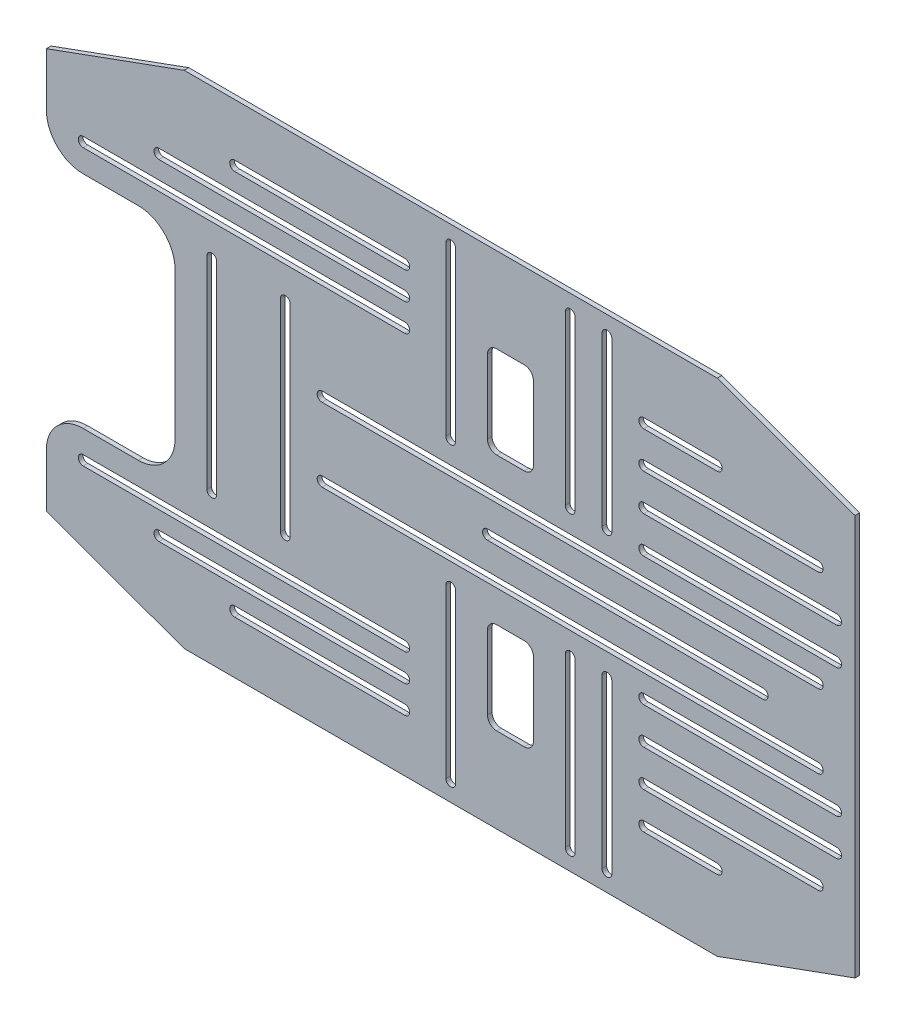
SolidWorks part; units mm, degrees
material "6061-T6 (SS)"
ref_plane "Front Plane" through (0, 0, 0) normal (0, 0, 1) x (1, 0, 0)
ref_plane "Top Plane" through (0, 0, 0) normal (0, 1, 0) x (1, 0, 0)
ref_plane "Right Plane" through (0, 0, 0) normal (1, 0, 0) x (0, 0, -1)
sketch "Sketch1" plane through (0, 0, 0) normal (0, 0, 1) x (1, 0, 0)
  line L0 (-279.4, 138.3894) -> (-184.2141, 173.0342)
  line L2 (-184.2141, 173.0342) -> (184.2141, 173.0342)
  line L3 (-254, 147.6342) -> (254, 147.6342) construction
  line L4 (184.2141, 173.0342) -> (279.4, 138.3894)
  line L5 (279.4, 138.3894) -> (279.4, -138.3894)
  line L10 (-254, 147.6342) -> (-254, -147.6342) construction
  line L11 (279.4, -138.3894) -> (184.2141, -173.0342)
  line L12 (184.2141, -173.0342) -> (-184.2141, -173.0342)
  line L13 (-254, -147.6342) -> (254, -147.6342) construction
  line L14 (-184.2141, -173.0342) -> (-279.4, -138.3894)
  line L16 (-279.4, -76.2) -> (-190.5, -76.2)
  line L17 (-190.5, -76.2) -> (-190.5, 76.2)
  line L18 (-190.5, 76.2) -> (-279.4, 76.2)
  line L19 (-279.4, 76.2) -> (-279.4, 138.3894)
  line L20 (254, 147.6342) -> (254, -147.6342) construction
  line L24 (-279.4, -138.3894) -> (-279.4, -76.2)
  point P6 (0, 147.6342)
  point P7 (-254, 0)
  point P13 (-190.5, 0)
  dimension "D1" = 508
  dimension "D2" = 295.2684
  dimension "D3" = 20
  dimension "D4" = 20
  dimension "D5" = 20
  dimension "D6" = 20
  dimension "D7" = 25.4
  dimension "D8" = 25.4
  dimension "D9" = 25.4
  dimension "D10" = 152.4
  dimension "D11" = 88.9
extrude "Boss-Extrude1" add sketch "Sketch1" along normal blind 3.175
fillet "Fillet3" radius 25.4 4 edges at (-279.4, 76.2, 1.5875) (-190.5, 76.2, 1.5875) (-190.5, -76.2, 1.5875) (-279.4, -76.2, 1.5875)
sketch "Sketch4" plane through (0, 0, 3.175) normal (0, 0, 1) x (1, 0, 0)
  line L0 (-254, 95.25) -> (-31.75, 95.25) construction
  line L1 (-254, 98.6282) -> (-31.75, 98.6282)
  line L2 (-254, 91.8718) -> (-31.75, 91.8718)
  line L3 (-201.6606, 114.3) -> (-31.75, 114.3) construction
  line L4 (-201.6606, 117.6782) -> (-31.75, 117.6782)
  line L5 (-201.6606, 110.9218) -> (-31.75, 110.9218)
  line L6 (-149.3211, 133.35) -> (-31.75, 133.35) construction
  line L7 (-149.3211, 136.7282) -> (-31.75, 136.7282)
  line L8 (-149.3211, 129.9718) -> (-31.75, 129.9718)
  line L9 (-165.1, 69.85) -> (-165.1, -69.85) construction
  line L10 (-161.7218, 69.85) -> (-161.7218, -69.85)
  line L11 (-168.4782, 69.85) -> (-168.4782, -69.85)
  line L12 (-114.3, 69.85) -> (-114.3, -69.85) construction
  line L13 (-110.9218, 69.85) -> (-110.9218, -69.85)
  line L14 (-117.6782, 69.85) -> (-117.6782, -69.85)
  line L15 (-254, 76.2) -> (-215.9, 76.2) construction
  line L16 (254, 95.25) -> (184.2141, 120.65) construction
  line L17 (-254, 95.25) -> (-149.3211, 133.35) construction
  line L18 (-184.2141, 173.0342) -> (-279.4, 138.3894) construction
  line L19 (279.4, 0) -> (-279.4, 0) construction
  line L20 (279.4, -138.3894) -> (279.4, 138.3894) construction
  line L21 (0, -12.6623) -> (0, 49987.3377) construction
  line L22 (-279.4, 138.3894) -> (-279.4, 101.6) construction
  line L23 (0, 160.3342) -> (0, 44.45) construction
  line L24 (31.75, 114.3) -> (50.8, 114.3)
  line L25 (25.4, 107.95) -> (25.4, 57.15)
  line L26 (31.75, 50.8) -> (50.8, 50.8)
  line L27 (57.15, 107.95) -> (57.15, 57.15)
  line L28 (3.3782, 160.3342) -> (3.3782, 44.45)
  line L29 (-3.3782, 160.3342) -> (-3.3782, 44.45)
  line L30 (-88.9, 25.4) -> (254, 25.4) construction
  line L31 (-88.9, 28.7782) -> (254, 28.7782)
  line L32 (-88.9, 22.0218) -> (254, 22.0218)
  line L33 (82.55, 44.45) -> (82.55, 160.3342) construction
  line L34 (79.1718, 44.45) -> (79.1718, 160.3342)
  line L35 (85.9282, 44.45) -> (85.9282, 160.3342)
  line L36 (107.95, 160.3342) -> (107.95, 44.45) construction
  line L37 (111.3282, 160.3342) -> (111.3282, 44.45)
  line L38 (104.5718, 160.3342) -> (104.5718, 44.45)
  line L39 (133.35, 120.65) -> (184.2141, 120.65) construction
  line L40 (133.35, 124.0282) -> (184.2141, 124.0282)
  line L41 (133.35, 117.2718) -> (184.2141, 117.2718)
  line L42 (133.35, 95.25) -> (254, 95.25) construction
  line L43 (133.35, 98.6282) -> (254, 98.6282)
  line L44 (133.35, 91.8718) -> (254, 91.8718)
  line L45 (133.35, 69.85) -> (266.7, 69.85) construction
  line L46 (133.35, 73.2282) -> (266.7, 73.2282)
  line L47 (133.35, 66.4718) -> (266.7, 66.4718)
  line L48 (133.35, 44.45) -> (266.7, 44.45) construction
  line L49 (133.35, 47.8282) -> (266.7, 47.8282)
  line L50 (133.35, 41.0718) -> (266.7, 41.0718)
  line L51 (279.4, 138.3894) -> (184.2141, 173.0342) construction
  line L52 (184.2141, 173.0342) -> (-184.2141, 173.0342) construction
  line L53 (-190.5, 50.8) -> (-190.5, -50.8) construction
  line L54 (-254, -95.25) -> (-31.75, -95.25) construction
  line L55 (-254, -98.6282) -> (-31.75, -98.6282)
  line L56 (-254, -91.8718) -> (-31.75, -91.8718)
  line L57 (-201.6606, -114.3) -> (-31.75, -114.3) construction
  line L58 (-201.6606, -117.6782) -> (-31.75, -117.6782)
  line L59 (-201.6606, -110.9218) -> (-31.75, -110.9218)
  line L60 (-149.3211, -133.35) -> (-31.75, -133.35) construction
  line L61 (-149.3211, -136.7282) -> (-31.75, -136.7282)
  line L62 (-149.3211, -129.9718) -> (-31.75, -129.9718)
  line L63 (0, -160.3342) -> (0, -44.45) construction
  line L64 (3.3782, -160.3342) -> (3.3782, -44.45)
  line L65 (-3.3782, -160.3342) -> (-3.3782, -44.45)
  line L66 (-88.9, -25.4) -> (254, -25.4) construction
  line L67 (-88.9, -28.7782) -> (254, -28.7782)
  line L68 (-88.9, -22.0218) -> (254, -22.0218)
  line L69 (82.55, -44.45) -> (82.55, -160.3342) construction
  line L70 (79.1718, -44.45) -> (79.1718, -160.3342)
  line L71 (85.9282, -44.45) -> (85.9282, -160.3342)
  line L72 (107.95, -160.3342) -> (107.95, -44.45) construction
  line L73 (111.3282, -160.3342) -> (111.3282, -44.45)
  line L74 (104.5718, -160.3342) -> (104.5718, -44.45)
  line L75 (133.35, -120.65) -> (184.2141, -120.65) construction
  line L76 (133.35, -124.0282) -> (184.2141, -124.0282)
  line L77 (133.35, -117.2718) -> (184.2141, -117.2718)
  line L78 (133.35, -95.25) -> (254, -95.25) construction
  line L79 (133.35, -98.6282) -> (254, -98.6282)
  line L80 (133.35, -91.8718) -> (254, -91.8718)
  line L81 (133.35, -69.85) -> (266.7, -69.85) construction
  line L82 (133.35, -73.2282) -> (266.7, -73.2282)
  line L83 (133.35, -66.4718) -> (266.7, -66.4718)
  line L84 (133.35, -44.45) -> (266.7, -44.45) construction
  line L85 (133.35, -47.8282) -> (266.7, -47.8282)
  line L86 (133.35, -41.0718) -> (266.7, -41.0718)
  line L87 (57.15, -107.95) -> (57.15, -57.15)
  line L88 (31.75, -50.8) -> (50.8, -50.8)
  line L89 (25.4, -107.95) -> (25.4, -57.15)
  line L90 (31.75, -114.3) -> (50.8, -114.3)
  line L91 (25.4, 0) -> (215.9, 0) construction
  line L92 (25.4, 3.3782) -> (215.9, 3.3782)
  line L93 (25.4, -3.3782) -> (215.9, -3.3782)
  arc A0 (-254, 98.6282) -> (-254, 91.8718) centre (-254, 95.25) ccw
  arc A1 (-31.75, 91.8718) -> (-31.75, 98.6282) centre (-31.75, 95.25) ccw
  arc A2 (-201.6606, 117.6782) -> (-201.6606, 110.9218) centre (-201.6606, 114.3) ccw
  arc A3 (-31.75, 110.9218) -> (-31.75, 117.6782) centre (-31.75, 114.3) ccw
  arc A4 (-149.3211, 136.7282) -> (-149.3211, 129.9718) centre (-149.3211, 133.35) ccw
  arc A5 (-31.75, 129.9718) -> (-31.75, 136.7282) centre (-31.75, 133.35) ccw
  arc A6 (-161.7218, 69.85) -> (-168.4782, 69.85) centre (-165.1, 69.85) ccw
  arc A7 (-168.4782, -69.85) -> (-161.7218, -69.85) centre (-165.1, -69.85) ccw
  arc A8 (-110.9218, 69.85) -> (-117.6782, 69.85) centre (-114.3, 69.85) ccw
  arc A9 (-117.6782, -69.85) -> (-110.9218, -69.85) centre (-114.3, -69.85) ccw
  arc A10 (-254, -98.6282) -> (-254, -91.8718) centre (-254, -95.25) cw
  arc A11 (-31.75, -91.8718) -> (-31.75, -98.6282) centre (-31.75, -95.25) cw
  arc A12 (3.3782, 160.3342) -> (-3.3782, 160.3342) centre (0, 160.3342) ccw
  arc A13 (-3.3782, 44.45) -> (3.3782, 44.45) centre (0, 44.45) ccw
  arc A14 (-88.9, 28.7782) -> (-88.9, 22.0218) centre (-88.9, 25.4) ccw
  arc A15 (254, 22.0218) -> (254, 28.7782) centre (254, 25.4) ccw
  arc A16 (79.1718, 44.45) -> (85.9282, 44.45) centre (82.55, 44.45) ccw
  arc A17 (85.9282, 160.3342) -> (79.1718, 160.3342) centre (82.55, 160.3342) ccw
  arc A18 (111.3282, 160.3342) -> (104.5718, 160.3342) centre (107.95, 160.3342) ccw
  arc A19 (104.5718, 44.45) -> (111.3282, 44.45) centre (107.95, 44.45) ccw
  arc A20 (133.35, 124.0282) -> (133.35, 117.2718) centre (133.35, 120.65) ccw
  arc A21 (184.2141, 117.2718) -> (184.2141, 124.0282) centre (184.2141, 120.65) ccw
  arc A22 (133.35, 98.6282) -> (133.35, 91.8718) centre (133.35, 95.25) ccw
  arc A23 (254, 91.8718) -> (254, 98.6282) centre (254, 95.25) ccw
  arc A24 (133.35, 73.2282) -> (133.35, 66.4718) centre (133.35, 69.85) ccw
  arc A25 (266.7, 66.4718) -> (266.7, 73.2282) centre (266.7, 69.85) ccw
  arc A26 (133.35, 47.8282) -> (133.35, 41.0718) centre (133.35, 44.45) ccw
  arc A27 (266.7, 41.0718) -> (266.7, 47.8282) centre (266.7, 44.45) ccw
  arc A28 (-201.6606, -117.6782) -> (-201.6606, -110.9218) centre (-201.6606, -114.3) cw
  arc A29 (-31.75, -110.9218) -> (-31.75, -117.6782) centre (-31.75, -114.3) cw
  arc A30 (-149.3211, -136.7282) -> (-149.3211, -129.9718) centre (-149.3211, -133.35) cw
  arc A31 (-31.75, -129.9718) -> (-31.75, -136.7282) centre (-31.75, -133.35) cw
  arc A32 (3.3782, -160.3342) -> (-3.3782, -160.3342) centre (0, -160.3342) cw
  arc A33 (-3.3782, -44.45) -> (3.3782, -44.45) centre (0, -44.45) cw
  arc A34 (-88.9, -28.7782) -> (-88.9, -22.0218) centre (-88.9, -25.4) cw
  arc A35 (254, -22.0218) -> (254, -28.7782) centre (254, -25.4) cw
  arc A36 (79.1718, -44.45) -> (85.9282, -44.45) centre (82.55, -44.45) cw
  arc A37 (85.9282, -160.3342) -> (79.1718, -160.3342) centre (82.55, -160.3342) cw
  arc A38 (111.3282, -160.3342) -> (104.5718, -160.3342) centre (107.95, -160.3342) cw
  arc A39 (104.5718, -44.45) -> (111.3282, -44.45) centre (107.95, -44.45) cw
  arc A40 (133.35, -124.0282) -> (133.35, -117.2718) centre (133.35, -120.65) cw
  arc A41 (184.2141, -117.2718) -> (184.2141, -124.0282) centre (184.2141, -120.65) cw
  arc A42 (133.35, -98.6282) -> (133.35, -91.8718) centre (133.35, -95.25) cw
  arc A43 (254, -91.8718) -> (254, -98.6282) centre (254, -95.25) cw
  arc A44 (133.35, -73.2282) -> (133.35, -66.4718) centre (133.35, -69.85) cw
  arc A45 (266.7, -66.4718) -> (266.7, -73.2282) centre (266.7, -69.85) cw
  arc A46 (133.35, -47.8282) -> (133.35, -41.0718) centre (133.35, -44.45) cw
  arc A47 (266.7, -41.0718) -> (266.7, -47.8282) centre (266.7, -44.45) cw
  arc A48 (25.4, 3.3782) -> (25.4, -3.3782) centre (25.4, 0) ccw
  arc A49 (215.9, -3.3782) -> (215.9, 3.3782) centre (215.9, 0) ccw
  arc A50 (25.4, -107.95) -> (31.75, -114.3) centre (31.75, -107.95) ccw
  arc A51 (31.75, -50.8) -> (25.4, -57.15) centre (31.75, -57.15) ccw
  arc A52 (57.15, -57.15) -> (50.8, -50.8) centre (50.8, -57.15) ccw
  arc A53 (57.15, -107.95) -> (50.8, -114.3) centre (50.8, -107.95) cw
  arc A54 (50.8, 50.8) -> (57.15, 57.15) centre (50.8, 57.15) ccw
  arc A55 (25.4, 57.15) -> (31.75, 50.8) centre (31.75, 57.15) ccw
  arc A56 (50.8, 114.3) -> (57.15, 107.95) centre (50.8, 107.95) cw
  arc A57 (31.75, 114.3) -> (25.4, 107.95) centre (31.75, 107.95) ccw
  point P2 (-142.875, 95.25)
  point P7 (-116.7053, 114.3)
  point P14 (-90.5356, 133.35)
  point P21 (-165.1, 0)
  point P28 (-114.3, 0)
  point P43 (0, 0)
  point P53 (0, 102.3921)
  point P62 (82.55, 25.4)
  point P69 (82.55, 102.3921)
  point P76 (107.95, 102.3921)
  point P83 (158.782, 120.65)
  point P90 (193.675, 95.25)
  point P97 (200.025, 69.85)
  point P104 (200.025, 44.45)
  point P115 (120.65, 0)
  point P125 (25.4, -114.3)
  point P131 (25.4, -50.8)
  point P136 (-142.875, -95.25)
  point P143 (-116.7053, -114.3)
  point P150 (-90.5356, -133.35)
  point P157 (0, -102.3921)
  point P164 (82.55, -25.4)
  point P171 (82.55, -102.3921)
  point P178 (107.95, -102.3921)
  point P185 (158.782, -120.65)
  point P192 (193.675, -95.25)
  point P199 (200.025, -69.85)
  point P206 (200.025, -44.45)
  point P214 (57.15, -50.8)
  point P219 (57.15, -114.3)
  point P222 (57.15, 50.8)
  point P225 (25.4, 50.8)
  point P228 (57.15, 114.3)
  point P231 (25.4, 114.3)
  dimension "D1" = 6.7564
  dimension "D23" = 6.35
  dimension "D2" = 19.05
  dimension "D3" = 19.05
  dimension "D4" = 19.05
  dimension "D5" = 50.8
  dimension "D6" = 31.75
  dimension "D7" = 31.75
  dimension "D8" = 63.5
  dimension "D9" = 25.4
  dimension "D10" = 25.4
  dimension "D11" = 25.4
  dimension "D12" = 25.4
  dimension "D13" = 25.4
  dimension "D14" = 25.4
  dimension "D15" = 25.4
  dimension "D16" = 12.7
  dimension "D17" = 12.7
  dimension "D18" = 25.4
  dimension "D19" = 25.4
  dimension "D20" = 25.4
  dimension "D21" = 25.4
  dimension "D22" = 63.5
extrude "Cut-Extrude3" cut sketch "Sketch4" against normal through all
ref_plane "MidPlane" through (0, 0, 1.5875) normal (0, 0, 1) x (1, 0, 0)
